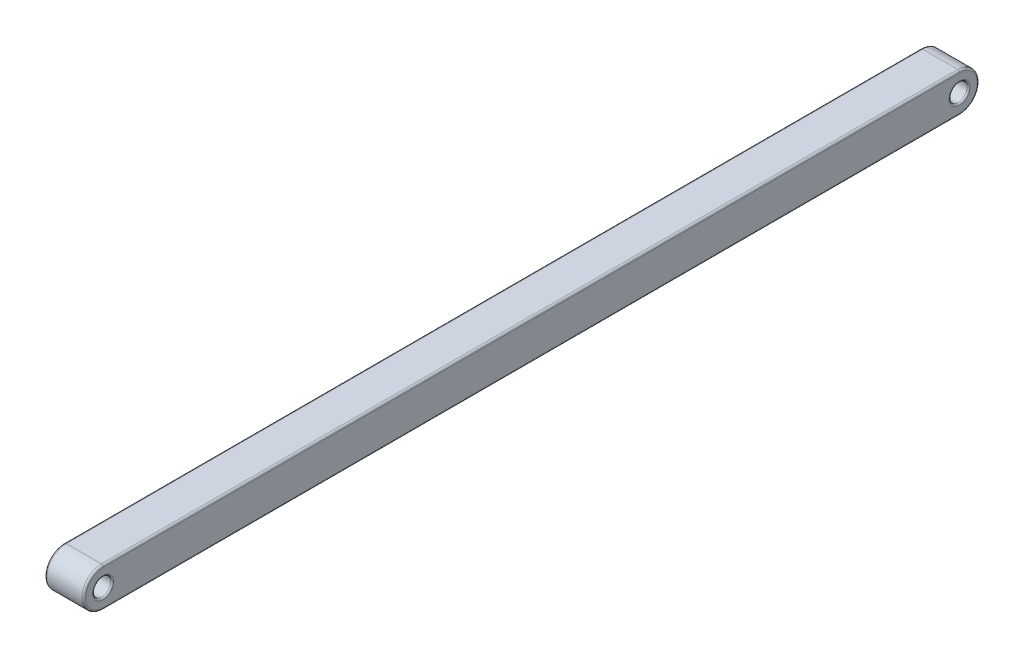
SolidWorks part; units mm, degrees
ref_plane "Front Plane" through (0, 0, 0) normal (0, 0, 1) x (1, 0, 0)
ref_plane "Top Plane" through (0, 0, 0) normal (0, 1, 0) x (1, 0, 0)
ref_plane "Right Plane" through (0, 0, 0) normal (1, 0, 0) x (0, 0, -1)
sketch "Sketch1" plane through (0, 0, 0) normal (1, 0, 0) x (0, 0, -1)
  line L1 (0, 0) -> (55, 0)
  line L3 (0, -2.5) -> (55, -2.5)
  line L8 (0, 0) -> (0, -2.5) construction
  line L12 (55, 0) -> (55, -2.5) construction
  circle A0 centre (0, -1.25) radius 0.575
  arc A1 (0, -2.5) -> (0, 0) centre (0, -1.25) cw
  circle A2 centre (55, -1.25) radius 0.575
  arc A3 (55, 0) -> (55, -2.5) centre (55, -1.25) cw
  dimension "D1" = 1.15
  dimension "D4" = 1.15
  dimension "D5" = 55
  dimension "D6" = 2.5
extrude "Boss-Extrude1" add sketch "Sketch1" along normal blind 2.5
fillet "Fillet1" radius 0.125 8 edges at (2.5, -2.5, -27.5) (0, -2.5, -27.5) (0, 0, -27.5) (2.5, 0, -27.5) (0, -1.25, -56.25) (2.5, -1.25, -56.25) (0, -1.25, 1.25) (2.5, -1.25, 1.25)
fillet "Fillet2" radius 0.1 4 edges at (0, -1.25, -0.575) (2.5, -1.25, -0.575) (0, -1.25, -55.575) (2.5, -1.25, -55.575)
